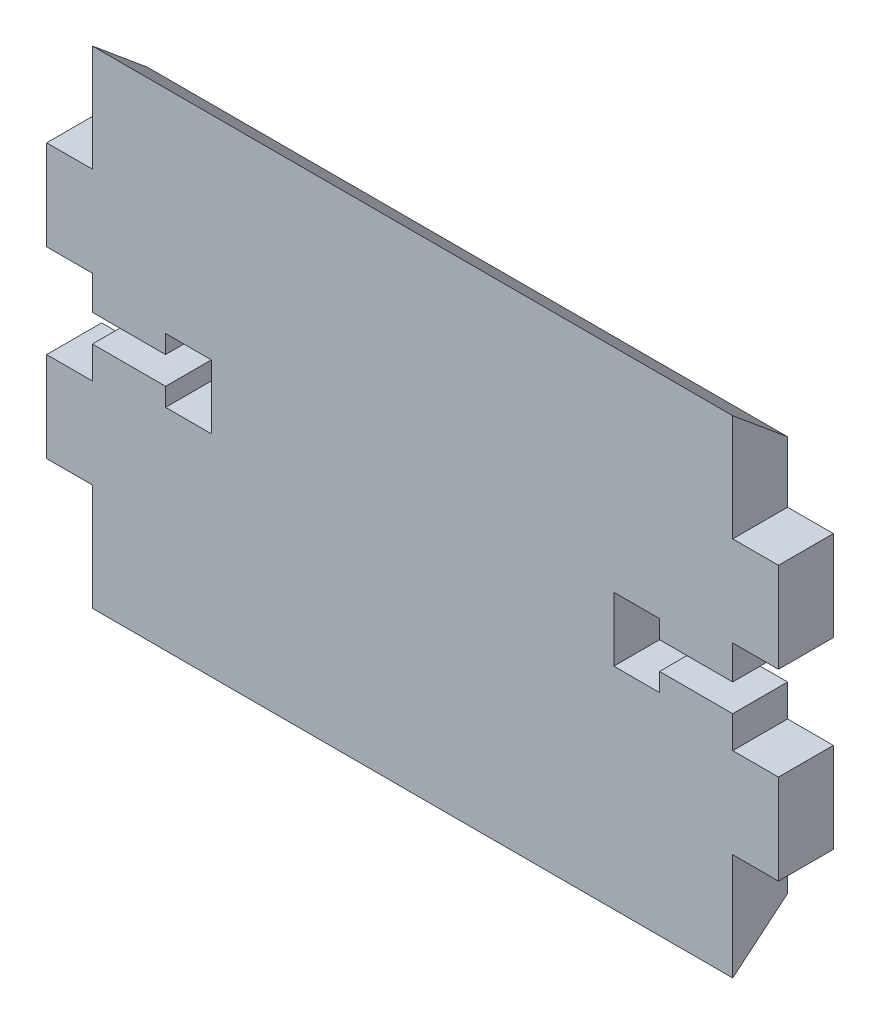
SolidWorks part; units mm, degrees
material "Cedro"
ref_plane "Plano frontal" through (0, 0, 0) normal (0, 0, 1) x (1, 0, 0)
ref_plane "Plano superior" through (0, 0, 0) normal (0, 1, 0) x (1, 0, 0)
ref_plane "Plano direito" through (0, 0, 0) normal (1, 0, 0) x (0, 0, -1)
sketch "Model" plane through (0, 0, 0) normal (0, 0, 1) x (1, 0, 0)
  line L0 (35, -42.315) -> (35, -54.735)
  line L1 (35, 0) -> (-35, 0)
  line L2 (-35, 0) -> (-35, -12.415)
  line L3 (-35, -12.415) -> (-40, -12.415)
  line L4 (-40, -12.415) -> (-40, -22.265)
  line L5 (-40, -22.265) -> (-35, -22.265)
  line L6 (-35, -22.265) -> (-35, -25.965)
  line L7 (-35, -25.965) -> (-27, -25.965)
  line L8 (-27, -25.965) -> (-27, -23.965)
  line L9 (-27, -23.965) -> (-22, -23.965)
  line L10 (-22, -23.965) -> (-22, -30.965)
  line L11 (-22, -30.965) -> (-27, -30.965)
  line L12 (-27, -30.965) -> (-27, -28.965)
  line L13 (-27, -28.965) -> (-35, -28.965)
  line L14 (-35, -28.965) -> (-35, -32.465)
  line L15 (-35, -32.465) -> (-40, -32.465)
  line L16 (-40, -32.465) -> (-40, -42.315)
  line L17 (-40, -42.315) -> (-35, -42.315)
  line L18 (-35, -42.315) -> (-35, -54.735)
  line L19 (0, -54.735) -> (0, 0) construction
  line L20 (40, -42.315) -> (35, -42.315)
  line L21 (40, -32.465) -> (40, -42.315)
  line L22 (35, -32.465) -> (40, -32.465)
  line L23 (35, -28.965) -> (35, -32.465)
  line L24 (27, -28.965) -> (35, -28.965)
  line L25 (27, -30.965) -> (27, -28.965)
  line L26 (22, -30.965) -> (27, -30.965)
  line L27 (22, -23.965) -> (22, -30.965)
  line L28 (27, -23.965) -> (22, -23.965)
  line L29 (27, -25.965) -> (27, -23.965)
  line L30 (35, -25.965) -> (27, -25.965)
  line L31 (35, -22.265) -> (35, -25.965)
  line L32 (40, -22.265) -> (35, -22.265)
  line L33 (40, -12.415) -> (40, -22.265)
  line L34 (35, -12.415) -> (40, -12.415)
  line L35 (35, 0) -> (35, -12.415)
  line L68 (-35, -54.735) -> (35, -54.735)
  dimension "D2" = 5
  dimension "D3" = 12.42
  dimension "D4" = 5
  dimension "D5" = 8
  dimension "D6" = 9.85
  dimension "D7" = 5
  dimension "D8" = 8
  dimension "D9" = 5
  dimension "D11" = 3
  dimension "D12" = 9.85
  dimension "D13" = 5
  dimension "D14" = 5
  dimension "D15" = 25.77
  dimension "D16" = 12.415
  dimension "D17" = 23.77
  dimension "D19" = 35
  dimension "D20" = 10.2
extrude "Ressalto-extrusão1" add sketch "Model" along normal blind 6
sketch "Esboço2" plane through (35, 0, 0) normal (1, 0, 0) x (0, 0, -1)
  line L0 (-6, -0.75) -> (0, -5.75)
  line L1 (-6, -12.415) -> (-6, 0) construction
  line L2 (0, -12.415) -> (0, 0) construction
  line L3 (0, -5.75) -> (0, 4.25)
  line L4 (0, 4.25) -> (-6, 4.25)
  line L5 (-6, 4.25) -> (-6, -0.75)
  line L6 (-6, 0) -> (0, 0) construction
  line L7 (16.1399, -27.37) -> (-31.1574, -27.37) construction
  line L8 (-6, -58.99) -> (-6, -53.99)
  line L9 (0, -58.99) -> (-6, -58.99)
  line L10 (0, -48.99) -> (0, -58.99)
  line L11 (-6, -53.99) -> (0, -48.99)
  dimension "D1" = 5
  dimension "D2" = 0.75
  dimension "D3" = 10
  dimension "D4" = 27.37
extrude "Corte-extrusão2" cut sketch "Esboço2" against normal through all
